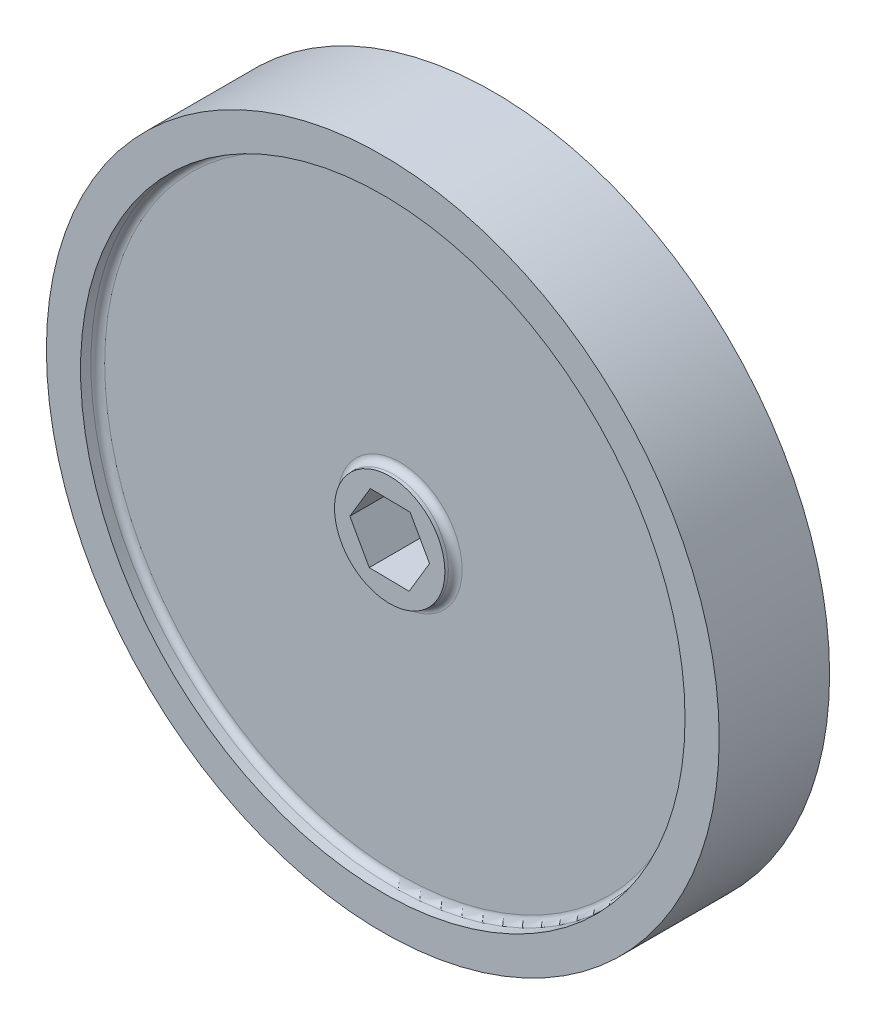
SolidWorks part; units mm, degrees
ref_plane "Front Plane" through (0, 0, 0) normal (0, 0, 1) x (1, 0, 0)
ref_plane "Top Plane" through (0, 0, 0) normal (0, 1, 0) x (1, 0, 0)
ref_plane "Right Plane" through (0, 0, 0) normal (1, 0, 0) x (0, 0, -1)
sketch "Sketch1" plane through (0, 0, 0) normal (0, 0, 1) x (1, 0, 0)
  line L1 (3.5692, -6.405) -> (7.3315, -0.1114)
  line L2 (7.3315, -0.1114) -> (3.7623, 6.2935)
  line L3 (3.7623, 6.2935) -> (-3.5692, 6.405)
  line L4 (-3.5692, 6.405) -> (-7.3315, 0.1114)
  line L5 (-7.3315, 0.1114) -> (-3.7623, -6.2935)
  line L6 (-3.7623, -6.2935) -> (3.5692, -6.405)
  circle A0 centre (0, 0) radius 61.9125
  circle A1 centre (0, 0) radius 6.35 construction
  dimension "D1" = 123.825
  dimension "D2" = 12.7
extrude "Boss-Extrude1" add sketch "Sketch1" along normal blind 20.32
sketch "Sketch2" plane through (0, 0, 20.32) normal (0, 0, 1) x (1, 0, 0)
  circle A0 centre (0, 0) radius 10.16
  circle A1 centre (0, 0) radius 55.626
  dimension "D1" = 20.32
  dimension "D2" = 111.252
extrude "Cut-Extrude1" cut sketch "Sketch2" against normal blind 3.175
sketch "Sketch3" plane through (0, 0, 0) normal (0, 0, -1) x (-1, 0, 0)
  circle A0 centre (0, 0) radius 55.626
  circle A1 centre (0, 0) radius 10.16
  dimension "D1" = 111.252
  dimension "D2" = 20.32
extrude "Cut-Extrude2" cut sketch "Sketch3" against normal blind 3.175
sketch "Sketch4" plane through (0, 0, 0) normal (0, 0, -1) x (-1, 0, 0)
  circle A0 centre (0, 0) radius 10.16
extrude "Cut-Extrude3" cut sketch "Sketch4" against normal blind 1.27
sketch "Sketch7" plane through (0, 0, 20.32) normal (0, 0, 1) x (1, 0, 0)
  circle A0 centre (0, 0) radius 10.16
extrude "Cut-Extrude5" cut sketch "Sketch7" against normal blind 1.27
fillet "Fillet1" radius 1.27 4 edges at (-10.16, 0, 3.175) (-55.626, 0, 3.175) (10.16, 0, 17.145) (55.626, 0, 17.145)
